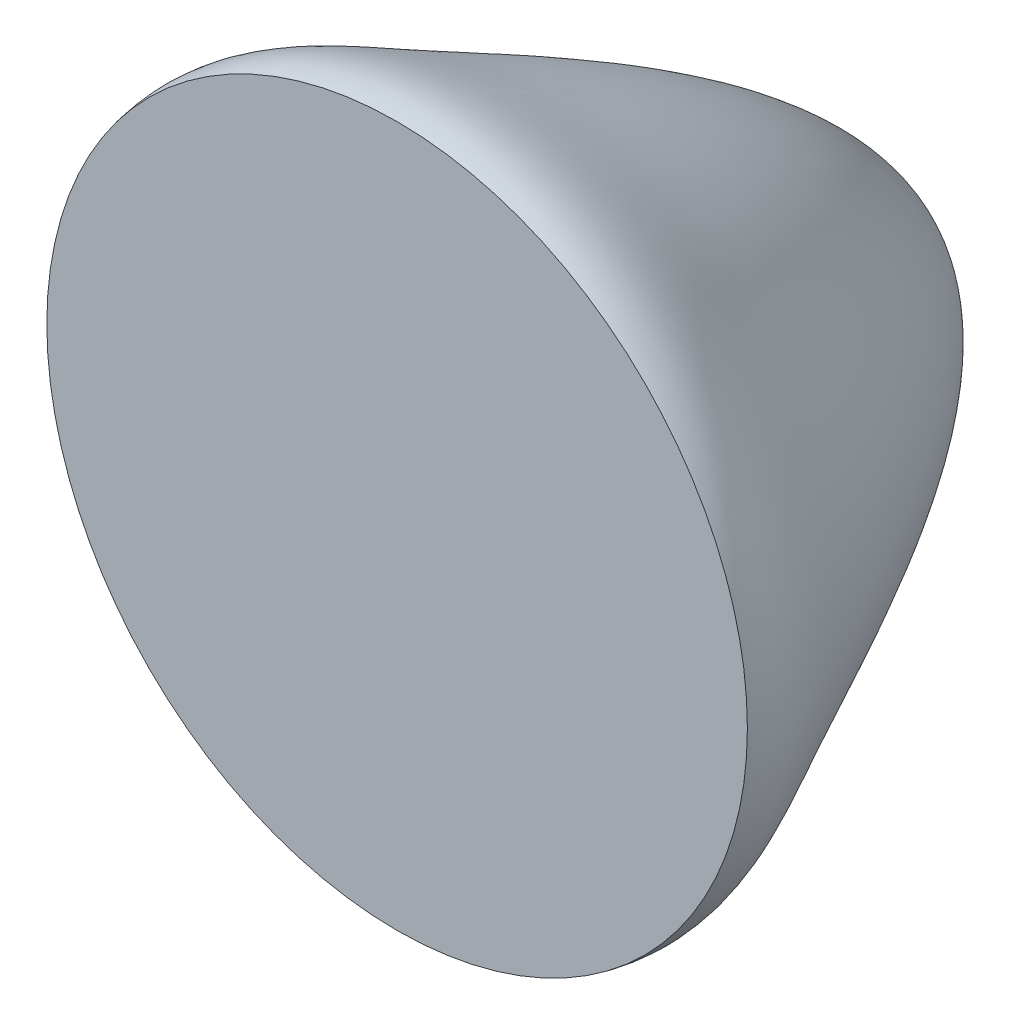
SolidWorks part; units mm, degrees
ref_plane "Front Plane" through (0, 0, 0) normal (0, 0, 1) x (1, 0, 0)
ref_plane "Top Plane" through (0, 0, 0) normal (0, 1, 0) x (1, 0, 0)
ref_plane "Right Plane" through (0, 0, 0) normal (1, 0, 0) x (0, 0, -1)
sketch "Sketch2" plane through (0, 0, 0) normal (1, 0, 0) x (0, 0, -1)
  line L0 (0, 0.8) -> (0, 0)
  line L1 (1.15, 0) -> (0, 0)
  line L2 (0, 0.8) -> (-0.4087, 0.7116) construction
  line L3 (1.15, 0) -> (1.15, -0.272) construction
  spline S0 degree 3 poles (0, 0.8) (0.0989, 0.8214) (0.3217, 0.6796) (1.15, 0.3197) (1.15, 0) knots 0 0 0 0 0.365919 1 1 1 1
  point P4 (1.8634, 0.8)
  point P6 (0.343, 0.6884)
  dimension "D1" = 0.8
  dimension "D2" = 1.15
revolve "Revolve1" add sketch "Sketch2" angle 360 about L1
